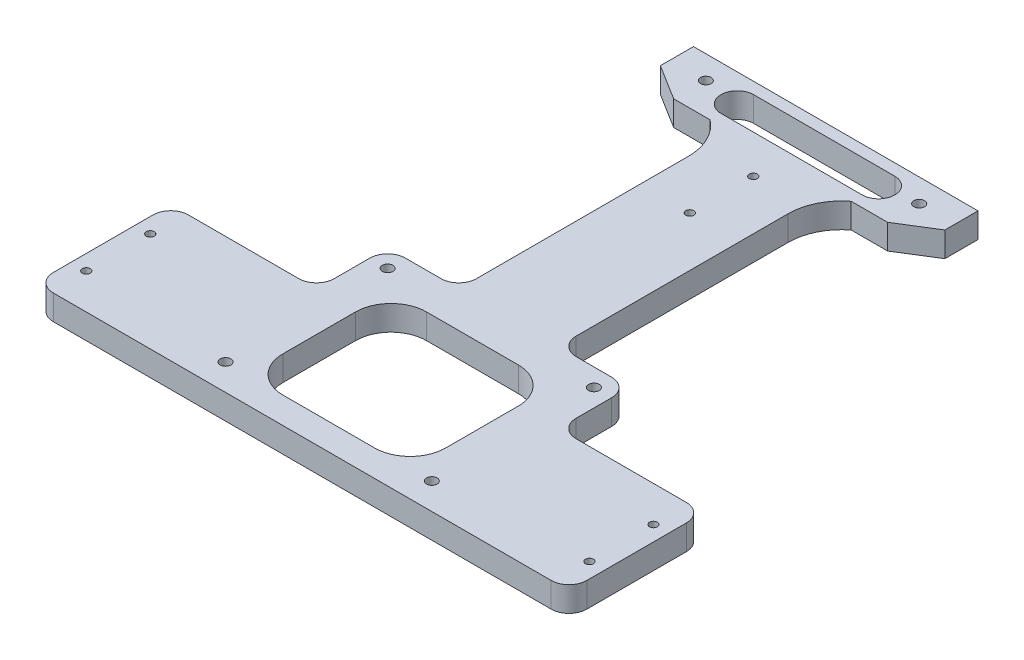
SolidWorks part; units mm, degrees
ref_plane "Front Plane" through (0, 0, 0) normal (0, 0, 1) x (1, 0, 0)
ref_plane "Top Plane" through (0, 0, 0) normal (0, 1, 0) x (1, 0, 0)
ref_plane "Right Plane" through (0, 0, 0) normal (1, 0, 0) x (0, 0, -1)
sketch "Sketch1" plane through (0, 0, 0) normal (0, 1, 0) x (1, 0, 0)
  line L8 (283.8254, -12.638) -> (247.8254, -12.638)
  line L10 (247.8254, -17.638) -> (247.8254, -12.638)
  line L11 (179.8254, -12.638) -> (179.8254, -17.638)
  line L12 (184.8254, -22.638) -> (242.8254, -22.638)
  line L32 (288.8254, -7.638) -> (288.8254, 20.362)
  line L33 (283.8254, 25.362) -> (252.8254, 25.362)
  line L34 (247.8254, 30.362) -> (247.8254, 40.362)
  line L37 (242.8254, 45.362) -> (232.8254, 45.362)
  line L38 (227.8254, 50.362) -> (227.8254, 117.362)
  line L39 (232.8254, 122.362) -> (242.8254, 122.362)
  line L40 (247.8254, 127.362) -> (247.8254, 132.362)
  line L41 (242.8254, 137.362) -> (184.8254, 137.362)
  line L42 (179.8254, 132.362) -> (179.8254, 127.362)
  line L43 (184.8254, 122.362) -> (194.8254, 122.362)
  line L44 (199.8254, 117.362) -> (199.8254, 50.362)
  line L45 (194.8254, 45.362) -> (184.8254, 45.362)
  line L46 (179.8254, 40.362) -> (179.8254, 30.362)
  line L47 (174.8254, 25.362) -> (143.8254, 25.362)
  line L48 (138.8254, 20.362) -> (138.8254, -7.638)
  line L49 (143.8254, -12.638) -> (179.8254, -12.638)
  arc A3 (283.8254, -12.638) -> (288.8254, -7.638) centre (283.8254, -7.638) ccw
  arc A4 (288.8254, 20.362) -> (283.8254, 25.362) centre (283.8254, 20.362) ccw
  arc A5 (252.8254, 25.362) -> (247.8254, 30.362) centre (252.8254, 30.362) cw
  arc A6 (247.8254, 40.362) -> (242.8254, 45.362) centre (242.8254, 40.362) ccw
  arc A7 (232.8254, 45.362) -> (227.8254, 50.362) centre (232.8254, 50.362) cw
  arc A8 (227.8254, 117.362) -> (232.8254, 122.362) centre (232.8254, 117.362) cw
  arc A9 (242.8254, 122.362) -> (247.8254, 127.362) centre (242.8254, 127.362) ccw
  arc A10 (247.8254, 132.362) -> (242.8254, 137.362) centre (242.8254, 132.362) ccw
  arc A11 (184.8254, 137.362) -> (179.8254, 132.362) centre (184.8254, 132.362) ccw
  arc A12 (179.8254, 127.362) -> (184.8254, 122.362) centre (184.8254, 127.362) ccw
  arc A13 (194.8254, 122.362) -> (199.8254, 117.362) centre (194.8254, 117.362) cw
  arc A14 (199.8254, 50.362) -> (194.8254, 45.362) centre (194.8254, 50.362) cw
  arc A15 (184.8254, 45.362) -> (179.8254, 40.362) centre (184.8254, 40.362) ccw
  arc A16 (179.8254, 30.362) -> (174.8254, 25.362) centre (174.8254, 30.362) cw
  arc A17 (143.8254, 25.362) -> (138.8254, 20.362) centre (143.8254, 20.362) ccw
  arc A18 (138.8254, -7.638) -> (143.8254, -12.638) centre (143.8254, -7.638) ccw
  arc A19 (242.8254, -22.638) -> (247.8254, -17.638) centre (242.8254, -17.638) ccw
  arc A20 (179.8254, -17.638) -> (184.8254, -22.638) centre (184.8254, -17.638) ccw
  point P2 (179.8254, -22.638)
  point P3 (252.8254, -22.638)
  point P57 (179.8254, -22.638)
  dimension "D1" = 5
extrude "Boss-Extrude3" add sketch "Sketch1" along normal blind 7
sketch "Sketch2" plane through (0, 7, 0) normal (0, 1, 0) x (1, 0, 0)
  line L0 (179.8254, -12.638) -> (247.8254, -12.638)
  line L21 (247.8254, -17.638) -> (247.8254, -12.638)
  line L22 (247.8254, -12.638) -> (283.8254, -12.638)
  line L23 (288.8254, -7.638) -> (288.8254, 20.362)
  line L24 (283.8254, 25.362) -> (252.8254, 25.362)
  line L25 (247.8254, 30.362) -> (247.8254, 40.362)
  line L26 (242.8254, 45.362) -> (232.8254, 45.362)
  line L27 (227.8254, 50.362) -> (227.8254, 117.362)
  line L28 (232.8254, 122.362) -> (242.8254, 122.362)
  line L29 (247.8254, 127.362) -> (247.8254, 132.362)
  line L30 (242.8254, 137.362) -> (184.8254, 137.362)
  line L31 (179.8254, 132.362) -> (179.8254, 127.362)
  line L32 (184.8254, 122.362) -> (194.8254, 122.362)
  line L33 (199.8254, 117.362) -> (199.8254, 50.362)
  line L34 (194.8254, 45.362) -> (184.8254, 45.362)
  line L35 (179.8254, 40.362) -> (179.8254, 30.362)
  line L36 (174.8254, 25.362) -> (143.8254, 25.362)
  line L37 (138.8254, 20.362) -> (138.8254, -7.638)
  line L38 (143.8254, -12.638) -> (179.8254, -12.638)
  line L39 (179.8254, -12.638) -> (179.8254, -17.638)
  line L40 (184.8254, -22.638) -> (242.8254, -22.638)
  line L41 (247.8254, -17.638) -> (247.8254, -12.638)
  line L59 (179.8254, -12.638) -> (179.8254, -17.638)
  line L60 (184.8254, -22.638) -> (242.8254, -22.638)
  arc A18 (242.8254, -22.638) -> (247.8254, -17.638) centre (242.8254, -17.638) ccw
  arc A19 (283.8254, -12.638) -> (288.8254, -7.638) centre (283.8254, -7.638) ccw
  arc A20 (288.8254, 20.362) -> (283.8254, 25.362) centre (283.8254, 20.362) ccw
  arc A21 (247.8254, 30.362) -> (252.8254, 25.362) centre (252.8254, 30.362) ccw
  arc A22 (247.8254, 40.362) -> (242.8254, 45.362) centre (242.8254, 40.362) ccw
  arc A23 (227.8254, 50.362) -> (232.8254, 45.362) centre (232.8254, 50.362) ccw
  arc A24 (232.8254, 122.362) -> (227.8254, 117.362) centre (232.8254, 117.362) ccw
  arc A25 (242.8254, 122.362) -> (247.8254, 127.362) centre (242.8254, 127.362) ccw
  arc A26 (247.8254, 132.362) -> (242.8254, 137.362) centre (242.8254, 132.362) ccw
  arc A27 (184.8254, 137.362) -> (179.8254, 132.362) centre (184.8254, 132.362) ccw
  arc A28 (179.8254, 127.362) -> (184.8254, 122.362) centre (184.8254, 127.362) ccw
  arc A29 (199.8254, 117.362) -> (194.8254, 122.362) centre (194.8254, 117.362) ccw
  arc A30 (194.8254, 45.362) -> (199.8254, 50.362) centre (194.8254, 50.362) ccw
  arc A31 (184.8254, 45.362) -> (179.8254, 40.362) centre (184.8254, 40.362) ccw
  arc A32 (174.8254, 25.362) -> (179.8254, 30.362) centre (174.8254, 30.362) ccw
  arc A33 (143.8254, 25.362) -> (138.8254, 20.362) centre (143.8254, 20.362) ccw
  arc A34 (138.8254, -7.638) -> (143.8254, -12.638) centre (143.8254, -7.638) ccw
  arc A35 (179.8254, -17.638) -> (184.8254, -22.638) centre (184.8254, -17.638) ccw
  arc A36 (242.8254, -22.638) -> (247.8254, -17.638) centre (242.8254, -17.638) ccw
  arc A53 (179.8254, -17.638) -> (184.8254, -22.638) centre (184.8254, -17.638) ccw
  dimension "D1" = 0
extrude "Cut-Extrude1" cut sketch "Sketch2" against normal blind 10
sketch "Sketch3" plane through (0, 7, 0) normal (0, 1, 0) x (1, 0, 0)
  line L6 (143.8254, -12.638) -> (283.8254, -12.638) construction
  line L7 (236.7298, 25.2195) -> (236.7298, 4.7892)
  line L9 (200.921, 35.2195) -> (226.7298, 35.2195)
  line L10 (190.921, 25.2195) -> (190.921, 4.7892)
  line L11 (200.921, -5.2108) -> (226.7298, -5.2108)
  line L13 (213.8254, -5.2108) -> (213.8254, -12.638) construction
  circle A0 centre (143.0754, 15.362) radius 1.125
  circle A1 centre (143.0754, -2.638) radius 1.125
  circle A3 centre (284.5754, -2.638) radius 1.125
  circle A4 centre (284.5754, 15.362) radius 1.125
  arc A5 (190.921, 4.7892) -> (200.921, -5.2108) centre (200.921, 4.7892) ccw
  arc A6 (236.7298, 4.7892) -> (226.7298, -5.2108) centre (226.7298, 4.7892) cw
  arc A7 (236.7298, 25.2195) -> (226.7298, 35.2195) centre (226.7298, 25.2195) ccw
  arc A8 (190.921, 25.2195) -> (200.921, 35.2195) centre (200.921, 25.2195) cw
  dimension "D2" = 2.25
  dimension "D3" = 10
  dimension "D1" = 18
extrude "Cut-Extrude3" cut sketch "Sketch3" against normal through all both and the other way through all
sketch "Sketch4" plane through (0, 7, 0) normal (0, 1, 0) x (1, 0, 0)
  line L0 (247.8254, 127.362) -> (247.8254, 132.362) construction
  line L1 (233.6797, 121.8653) -> (243.8982, 121.8653)
  line L2 (243.8982, 121.8653) -> (253.8254, 128.0522)
  line L5 (242.8254, 137.362) -> (184.8254, 137.362) construction
  line L6 (199.8254, 109.976) -> (199.8254, 83.862)
  line L7 (173.8254, 137.362) -> (253.8254, 137.362)
  line L8 (199.8254, 117.362) -> (199.8254, 50.362) construction
  line L9 (199.8254, 83.862) -> (227.8254, 83.862)
  line L10 (227.8254, 50.362) -> (227.8254, 117.362) construction
  line L11 (227.8254, 83.862) -> (227.8254, 109.976)
  line L14 (213.8254, 190.862) -> (213.8254, 83.862) construction
  line L15 (253.8254, 128.0522) -> (253.8254, 137.362)
  line L16 (173.8254, 128.0522) -> (173.8254, 137.362)
  line L17 (183.7525, 121.8653) -> (173.8254, 128.0522)
  line L18 (193.971, 121.8653) -> (183.7525, 121.8653)
  arc A1 (233.6797, 121.8653) -> (227.8254, 109.976) centre (242.8254, 109.976) ccw
  arc A2 (193.971, 121.8653) -> (199.8254, 109.976) centre (184.8254, 109.976) cw
  circle A3 centre (183.8982, 129.862) radius 1.5
  circle A4 centre (243.8982, 129.862) radius 1.5
  point P8 (213.8254, 137.362)
  point P9 (213.8254, 137.362)
  point P18 (199.8254, 117.362)
  point P21 (227.8254, 117.362)
  point P28 (213.8254, 137.362)
  point P29 (247.8254, 129.862)
  dimension "D1" = 80
  dimension "D3" = 60
extrude "Boss-Extrude4" add sketch "Sketch4" against normal blind 7
sketch "Sketch5" plane through (0, 7, 0) normal (0, 1, 0) x (1, 0, 0)
  line L1 (253.8254, 137.362) -> (173.8254, 137.362) construction
  circle A0 centre (183.8254, 130.8322) radius 1.5
  circle A1 centre (243.8254, 130.8322) radius 1.5
  circle A2 centre (242.8254, 40.362) radius 1.5
  circle A3 centre (184.8254, 40.362) radius 1.5
  circle A4 centre (184.8254, -5.2108) radius 1.5
  circle A5 centre (242.8254, -5.2108) radius 1.5
  dimension "D1" = 60
extrude "Cut-Extrude4" cut sketch "Sketch5" against normal through all both
sketch "Sketch6" plane through (0, 7, 0) normal (0, 1, 0) x (1, 0, 0)
  line L2 (253.8254, 137.362) -> (173.8254, 137.362) construction
  circle A0 centre (284.5754, 15.362) radius 1.125 construction
  circle A1 centre (284.5754, 15.362) radius 1.125
  circle A2 centre (213.8254, 96.3292) radius 1.125
  circle A3 centre (213.8254, 114.1777) radius 1.125
  point P2 (213.8254, 114.1957)
  point P3 (213.5943, 114.1277)
  point P6 (213.8254, 137.362)
extrude "Cut-Extrude5" cut sketch "Sketch6" against normal through all both and the other way through all
sketch "Sketch7" plane through (0, 7, 0) normal (0, 1, 0) x (1, 0, 0)
  line L1 (193.971, 134.1069) -> (233.6797, 134.1069)
  line L3 (193.971, 124.9603) -> (233.6797, 124.9603)
  arc A2 (193.971, 134.1069) -> (193.971, 124.9603) centre (193.971, 129.5336) ccw
  arc A3 (233.6797, 124.9603) -> (233.6797, 134.1069) centre (233.6797, 129.5336) ccw
  point P4 (189.3978, 129.5336)
  point P5 (238.253, 129.5336)
  dimension "D2" = 48.8552
  dimension "D1" = 39.7087
extrude "Cut-Extrude6" cut sketch "Sketch7" against normal through all both
